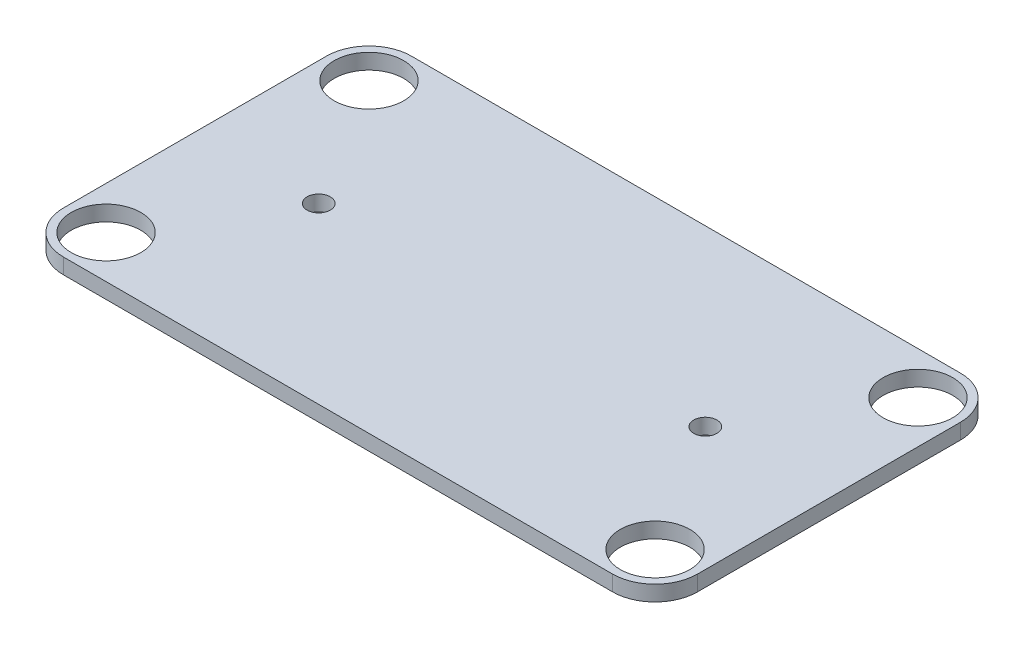
SolidWorks part; units mm, degrees
ref_plane "Plan de face" through (0, 0, 0) normal (0, 0, 1) x (1, 0, 0)
ref_plane "Plan de dessus" through (0, 0, 0) normal (0, 1, 0) x (1, 0, 0)
ref_plane "Plan de droite" through (0, 0, 0) normal (1, 0, 0) x (0, 0, -1)
sketch "Esquisse1" plane through (0, 0, 0) normal (0, 1, 0) x (1, 0, 0)
  line L1 (-41, 22.5) -> (41, 22.5)
  line L2 (-41, 22.5) -> (-41, -22.5)
  line L3 (-41, -22.5) -> (41, -22.5)
  line L4 (41, 22.5) -> (41, -22.5)
  circle A0 centre (-35.5, 17) radius 4.5
  circle A1 centre (35.5, 17) radius 4.5
  circle A2 centre (35.5, -17) radius 4.5
  circle A3 centre (-35.5, -17) radius 4.5
  circle A4 centre (-25, 0) radius 1.5
  circle A5 centre (25, 0) radius 1.5
  dimension "D7" = 9
  dimension "D10" = 9
  dimension "D13" = 9
  dimension "D16" = 9
  dimension "D19" = 3
  dimension "D20" = 3
  dimension "D1" = 45
  dimension "D2" = 22.5
  dimension "D3" = 82
  dimension "D4" = 41
  dimension "D5" = 5.5
  dimension "D6" = 5.5
  dimension "D8" = 5.5
  dimension "D9" = 5.5
  dimension "D11" = 5.5
  dimension "D12" = 5.5
  dimension "D14" = 5.5
  dimension "D15" = 5.5
  dimension "D17" = 25
  dimension "D18" = 50
  dimension "D21" = 22.5
  dimension "D22" = 22.5
extrude "Boss.-Extru.1" add sketch "Esquisse1" along normal blind 2
fillet "Congé1" radius 5.5 4 edges at (-41, 1, -22.5) (41, 1, -22.5) (41, 1, 22.5) (-41, 1, 22.5)
